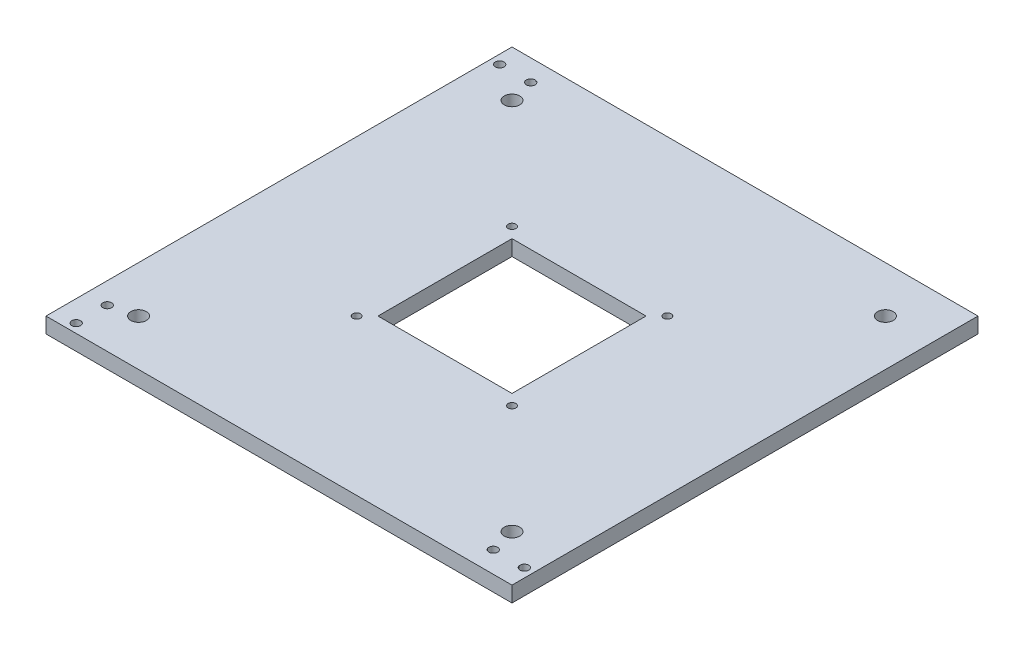
SolidWorks part; units mm, degrees
ref_plane "Front Plane" through (0, 0, 0) normal (0, 0, 1) x (1, 0, 0)
ref_plane "Top Plane" through (0, 0, 0) normal (0, 1, 0) x (1, 0, 0)
ref_plane "Right Plane" through (0, 0, 0) normal (1, 0, 0) x (0, 0, -1)
sketch "Sketch1" plane through (0, 0, 0) normal (0, 1, 0) x (1, 0, 0)
  line L1 (-95.25, -95.25) -> (95.25, -95.25)
  line L2 (-95.25, -95.25) -> (-95.25, 95.25)
  line L3 (-95.25, 95.25) -> (95.25, 95.25)
  line L4 (95.25, -95.25) -> (95.25, 95.25)
  line L5 (-15.875, -15.875) -> (15.875, -15.875)
  line L6 (-15.875, -15.875) -> (-15.875, 15.875)
  line L7 (-15.875, 15.875) -> (15.875, 15.875)
  line L8 (15.875, -15.875) -> (15.875, 15.875)
  circle A0 centre (-11.303, 11.303) radius 1.905
  circle A1 centre (-11.303, -11.303) radius 1.905
  circle A2 centre (11.303, 11.303) radius 1.905
  circle A3 centre (11.303, -11.303) radius 1.905
  circle A4 centre (-78.9, 86.55) radius 1.778
  circle A5 centre (-91.6, 86.55) radius 1.778
  circle A6 centre (91.6, -86.55) radius 1.778
  circle A7 centre (78.9, -86.55) radius 1.778
  circle A8 centre (-86.55, -78.9) radius 1.778
  circle A9 centre (-86.55, -91.6) radius 1.778
  circle A10 centre (0, 0) radius 6.35
  point P0 (0, 0)
  point P6 (0, 0)
  point P19 (-85.25, 92.9)
  point P24 (85.25, -92.9)
  point P29 (-92.9, -85.25)
  dimension "D5" = 4.572
  dimension "D10" = 12.7
  dimension "D18" = 12.7
  dimension "D1" = 190.5
  dimension "D2" = 190.5
  dimension "D3" = 31.75
  dimension "D4" = 31.75
  dimension "D6" = 4.572
  dimension "D7" = 4.572
  dimension "D8" = 92.9
  dimension "D9" = 85.25
  dimension "D11" = 4.572
  dimension "D12" = 6.35
  dimension "D13" = 6.35
  dimension "D14" = 92.9
  dimension "D15" = 85.25
  dimension "D16" = 6.35
  dimension "D17" = 6.35
  dimension "D19" = 85.25
  dimension "D20" = 92.9
  dimension "D21" = 6.35
  dimension "D22" = 6.35
  dimension "D23" = 12.7
extrude "Boss-Extrude1" add sketch "Sketch1" along normal blind 6.35 contours L4 L3 L2 L1 | A7 | A6 | A8 | A9 | A4 | A5 | A1 | A3 | A0 | A2
sketch "Sketch2" plane through (0, 0, 0) normal (0, -1, 0) x (1, 0, 0)
  line L0 (25.4, -25.4) -> (-25.4, -25.4) construction
  line L1 (25.4, 25.4) -> (25.4, -25.4) construction
  line L2 (-25.4, -25.4) -> (-25.4, 25.4) construction
  line L3 (25.4, -25.4) -> (-25.4, -25.4)
  line L4 (25.4, 25.4) -> (25.4, -25.4)
  line L5 (-25.4, -25.4) -> (-25.4, 25.4)
  line L6 (-25.4, 25.4) -> (25.4, 25.4) construction
  line L7 (-25.4, 25.4) -> (25.4, 25.4)
  line L8 (27.4, 27.4) -> (27.4, -27.4)
  line L9 (27.4, -27.4) -> (-27.4, -27.4)
  line L10 (-27.4, -27.4) -> (-27.4, 27.4)
  line L11 (-27.4, 27.4) -> (27.4, 27.4)
  dimension "D1" = 2
extrude "Cut-Extrude4" cut sketch "Sketch2" against normal blind 10 contours L9 L10 L11 L8
sketch "Sketch4" plane through (0, 0, 0) normal (0, -1, 0) x (1, 0, 0)
  circle A0 centre (-31.75, 31.75) radius 1.5875 construction
  circle A1 centre (31.75, 31.75) radius 1.5875 construction
  circle A2 centre (31.75, -31.75) radius 1.5875 construction
  circle A3 centre (-31.75, -31.75) radius 1.5875 construction
  circle A4 centre (-31.75, 31.75) radius 1.5875
  circle A5 centre (31.75, 31.75) radius 1.5875
  circle A6 centre (31.75, -31.75) radius 1.5875
  circle A7 centre (-31.75, -31.75) radius 1.5875
extrude "Cut-Extrude5" cut sketch "Sketch4" against normal blind 10 contours A5 | A7 | A4 | A6
sketch "Sketch5" plane through (0, 0, 0) normal (0, -1, 0) x (1, 0, 0)
  circle A0 centre (76.33, -76.33) radius 3.175 construction
  circle A1 centre (76.33, 76.33) radius 3.175 construction
  circle A2 centre (-76.33, -76.33) radius 3.175 construction
  circle A3 centre (-76.33, 76.33) radius 3.175 construction
  circle A4 centre (76.33, -76.33) radius 3.175
  circle A5 centre (76.33, 76.33) radius 3.175
  circle A6 centre (-76.33, -76.33) radius 3.175
  circle A7 centre (-76.33, 76.33) radius 3.175
extrude "Cut-Extrude6" cut sketch "Sketch5" against normal through all contours A4 | A5 | A6 | A7
